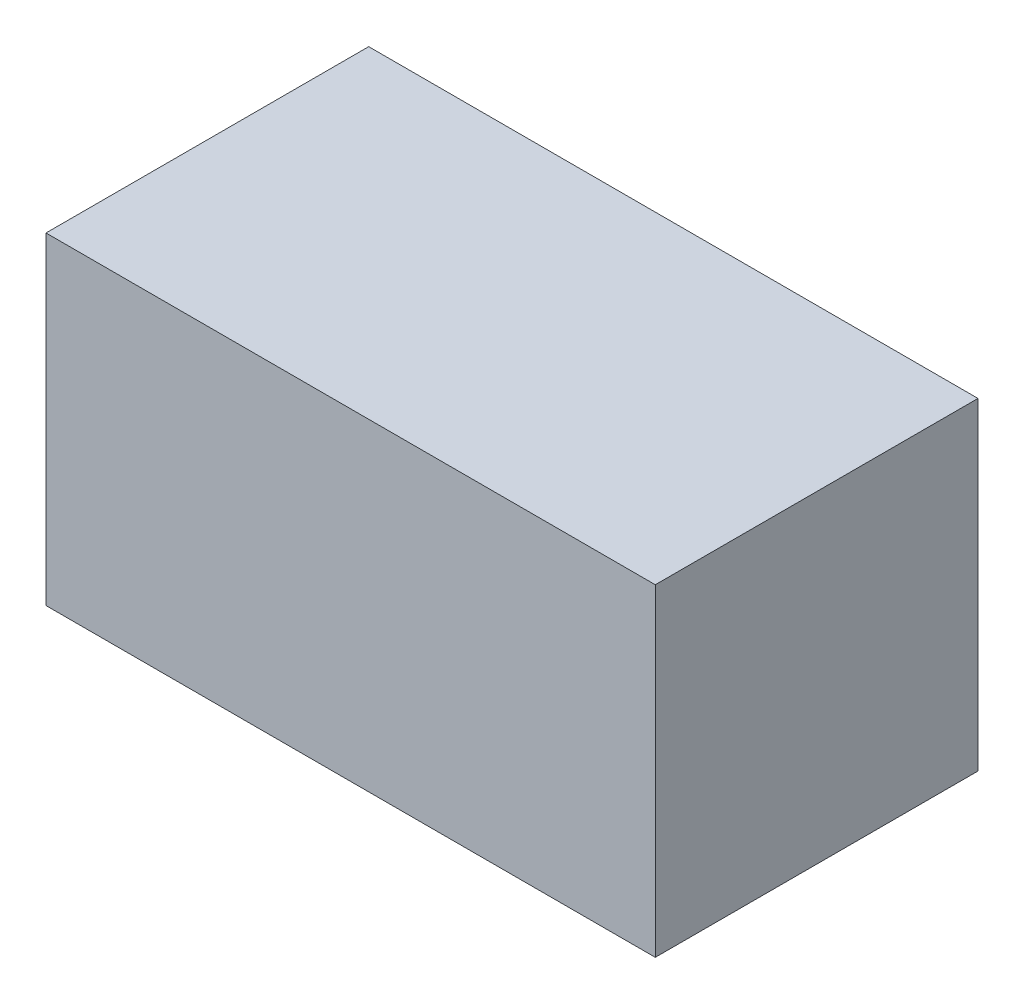
SolidWorks part; units mm, degrees
ref_plane "Front Plane" through (0, 0, 0) normal (0, 0, 1) x (1, 0, 0)
ref_plane "Top Plane" through (0, 0, 0) normal (0, 1, 0) x (1, 0, 0)
ref_plane "Right Plane" through (0, 0, 0) normal (1, 0, 0) x (0, 0, -1)
sketch "Sketch1" plane through (0, 0, 0) normal (1, 0, 0) x (0, 0, -1)
  line L1 (-0.908, 1.8161) -> (0.9081, 1.8161)
  line L2 (-0.908, 1.8161) -> (-0.9081, 0)
  line L3 (-0.9081, 0) -> (0.9081, 0)
  line L4 (0.9081, 1.8161) -> (0.9081, 0)
  point P4 (0, 0)
  dimension "D1" = 1.8161
extrude "Boss-Extrude1" add sketch "Sketch1" along normal mid plane 3.429
